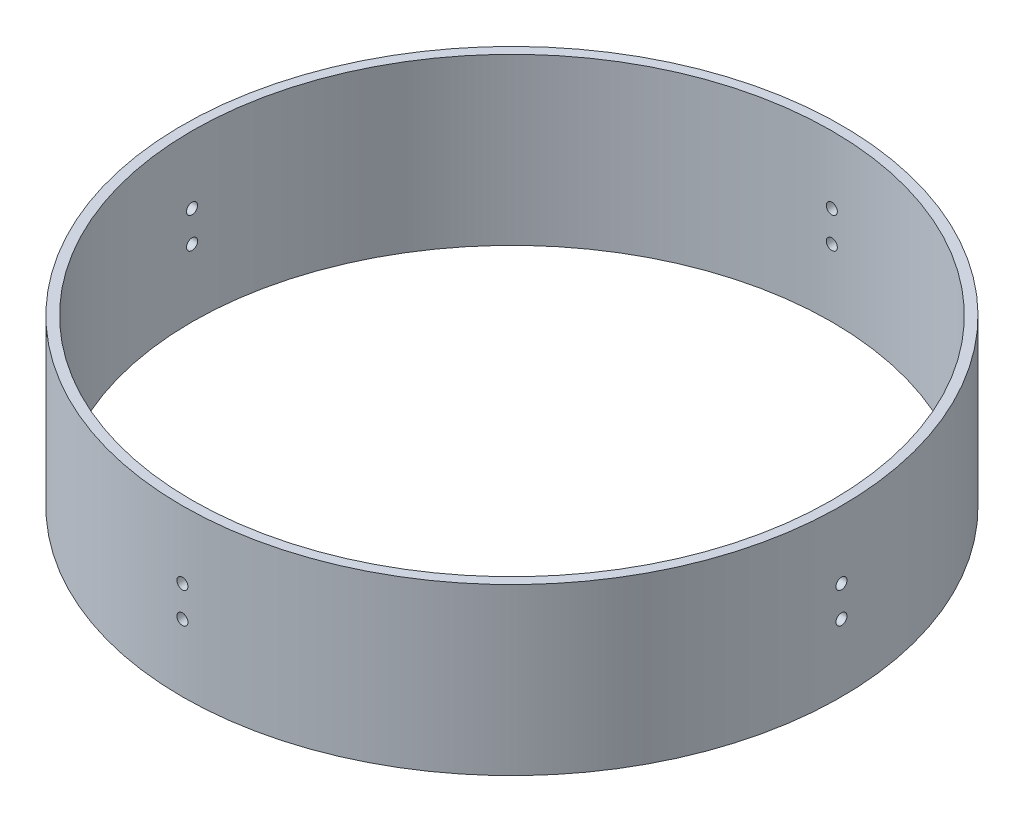
SolidWorks part; units mm, degrees
ref_plane "Front Plane" through (0, 0, 0) normal (0, 0, 1) x (1, 0, 0)
ref_plane "Top Plane" through (0, 0, 0) normal (0, 1, 0) x (1, 0, 0)
ref_plane "Right Plane" through (0, 0, 0) normal (1, 0, 0) x (0, 0, -1)
sketch "Sketch1" plane through (0, 0, 0) normal (0, 1, 0) x (1, 0, 0)
  circle A0 centre (0, 0) radius 75.8825
  dimension "D1" = 151.765
extrude "Boss-Extrude1" add sketch "Sketch1" along normal blind 38.1
sketch "Sketch2" plane through (0, 38.1, 0) normal (0, 1, 0) x (1, 0, 0)
  circle A0 centre (0, 0) radius 73.66
  dimension "D1" = 147.32
extrude "Cut-Extrude1" cut sketch "Sketch2" against normal blind 101.6
sketch "Sketch4" plane through (0, 0, 0) normal (1, 0, 0) x (0, 0, -1)
  line L0 (-75.8825, 19.05) -> (75.8825, 19.05) construction
  line L1 (-75.8825, 38.1) -> (-75.8825, 0) construction
  line L2 (75.8825, 0) -> (75.8825, 38.1) construction
  circle A0 centre (0, 22.606) radius 1.27
  circle A1 centre (0, 15.494) radius 1.27
  dimension "D1" = 2.54
  dimension "D2" = 7.112
extrude "Cut-Extrude3" cut sketch "Sketch4" against normal through all both and the other way through all
sketch "Sketch5" plane through (0, 0, 0) normal (0, 0, 1) x (1, 0, 0)
  line L0 (-75.8825, 19.05) -> (75.8825, 19.05) construction
  line L1 (-75.8825, 21.336) -> (-75.8825, 16.7639) construction
  line L2 (75.8825, 16.7639) -> (75.8825, 21.336) construction
  circle A0 centre (0, 15.494) radius 1.27
  circle A1 centre (0, 22.606) radius 1.27
  dimension "D1" = 2.54
  dimension "D2" = 7.112
extrude "Cut-Extrude4" cut sketch "Sketch5" against normal through all both and the other way through all
